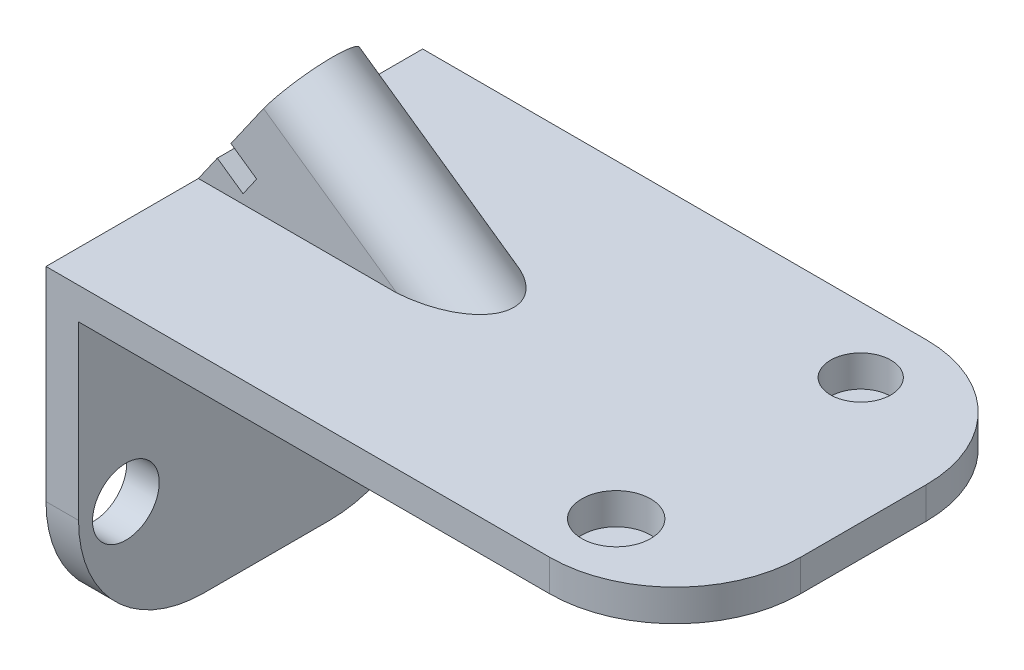
SolidWorks part; units mm, degrees
ref_plane "Front Plane" through (0, 0, 0) normal (0, 0, 1) x (1, 0, 0)
ref_plane "Top Plane" through (0, 0, 0) normal (0, 1, 0) x (1, 0, 0)
ref_plane "Right Plane" through (0, 0, 0) normal (1, 0, 0) x (0, 0, -1)
sketch "Sketch1" plane through (0, 0, 0) normal (0, 0, 1) x (1, 0, 0)
  line L0 (34.8768, 10.0959) -> (-50.9385, 10.0959)
  line L1 (-50.9385, 10.0959) -> (34.8768, 10.0959)
  line L2 (34.8768, 10.0959) -> (-11.4726, 66.5413)
  line L3 (-11.4726, 66.5413) -> (-50.9385, 10.0959)
extrude "Boss-Extrude1" add sketch "Sketch1" against normal blind 50 contours L2 L3 L0
sketch "Sketch2" plane through (-38.9542, 27.2363, 0) normal (-0.8195, 0.573, 0) x (0, 0, 1)
  line L0 (-37.847, -20.9145) -> (-37.847, 15.3073)
  line L1 (-50, -20.9145) -> (0, -20.9145) construction
  line L2 (-8.5468, 15.3073) -> (-8.5468, -20.9145)
  line L3 (-8.5468, -20.9145) -> (-37.847, -20.9145)
  line L5 (-50, 47.9596) -> (-37.847, 47.9596)
  line L6 (-50, 47.9596) -> (-50, -20.9145)
  line L7 (-50, -20.9145) -> (-37.847, -20.9145)
  line L8 (-37.847, 47.9596) -> (-37.847, -20.9145)
  line L9 (-37.847, 47.9596) -> (0, 47.9596)
  line L10 (-37.847, 47.9596) -> (-37.847, 28.259)
  line L11 (-37.847, 28.259) -> (0, 28.259)
  line L12 (0, 47.9596) -> (0, 28.259)
  line L13 (-8.5468, 28.259) -> (0, 28.259)
  line L14 (-8.5468, 28.259) -> (-8.5468, -20.9145)
  line L15 (-8.5468, -20.9145) -> (0, -20.9145)
  line L16 (0, 28.259) -> (0, -20.9145)
  arc A0 (-37.847, 15.3073) -> (-8.5468, 15.3073) centre (-23.1969, 12.7934) cw
  arc A1 (-37.847, 15.3073) -> (-8.5468, 15.3073) centre (-23.1969, 13.4976) cw
  line M1 (0, -20.9145) -> (0, 47.9596)
  line M2 (0, 47.9596) -> (-50, 47.9596)
  line M3 (-50, 47.9596) -> (-50, -20.9145)
  line M4 (-50, -20.9145) -> (0, -20.9145)
extrude "Cut-Extrude1" cut sketch "Sketch2" against normal blind 100 contours L8 L11 M1 M2 | L11 L14 L2 M4 M1 | L11 A1 L14 | L8 A1 L11 | L8 L0 M2 M3 M4
sketch "Sketch3" plane through (0, 0, 0) normal (0, 0, 1) x (1, 0, 0)
  line L0 (149.4861, 10.0959) -> (-50.9385, 10.0959)
  line L1 (-50.9385, 10.0959) -> (-50.9385, -94.7797)
  line L2 (-50.9385, -94.7797) -> (-40.5773, -94.7797)
  line L3 (-40.5773, -94.7797) -> (-40.5773, 0)
  line L4 (-40.5773, 0) -> (149.4861, 0)
  line L5 (149.4861, 0) -> (149.4861, 10.0959)
extrude "Boss-Extrude2" add sketch "Sketch3" against normal blind 80 and the other way blind 40
sketch "Sketch5" plane through (-38.9542, 27.2363, 0) normal (-0.8195, 0.573, 0) x (0, 0, 1)
  line L0 (-37.847, 15.3073) -> (-37.847, -20.9145) construction
  line L1 (-37.847, -2.8036) -> (-8.5468, -2.8036)
  line L2 (-37.847, -2.8036) -> (-37.847, -10.3851)
  line L3 (-37.847, -10.3851) -> (-8.5468, -10.3851)
  line L4 (-8.5468, -2.8036) -> (-8.5468, -10.3851)
  line L5 (-8.5468, 15.3073) -> (-8.5468, -20.9145) construction
  circle A0 centre (-23.1969, 13.4976) radius 6.1336
extrude "Cut-Extrude2" cut sketch "Sketch5" against normal blind 10
fillet "Fillet1" radius 40 2 edges at (-45.7579, -94.7797, -80) (-45.7579, -94.7797, 40)
fillet "Fillet2" radius 40 2 edges at (149.4861, 5.048, -80) (149.4861, 5.048, 40)
sketch "Sketch6" plane through (0, 10.0959, 0) normal (0, 1, 0) x (1, 0, 0)
  circle A0 centre (109.4861, 59.1371) radius 9.6126
  circle A1 centre (109.4861, -18.7714) radius 10.9786
extrude "Cut-Extrude3" cut sketch "Sketch6" against normal blind 10
sketch "Sketch7" plane through (-50.9385, 0, 0) normal (-1, 0, 0) x (0, 0, 1)
  circle A0 centre (-63.5437, -57.1641) radius 10.6288
  circle A1 centre (24.9151, -57.1641) radius 10.6288
extrude "Cut-Extrude4" cut sketch "Sketch7" against normal blind 20
